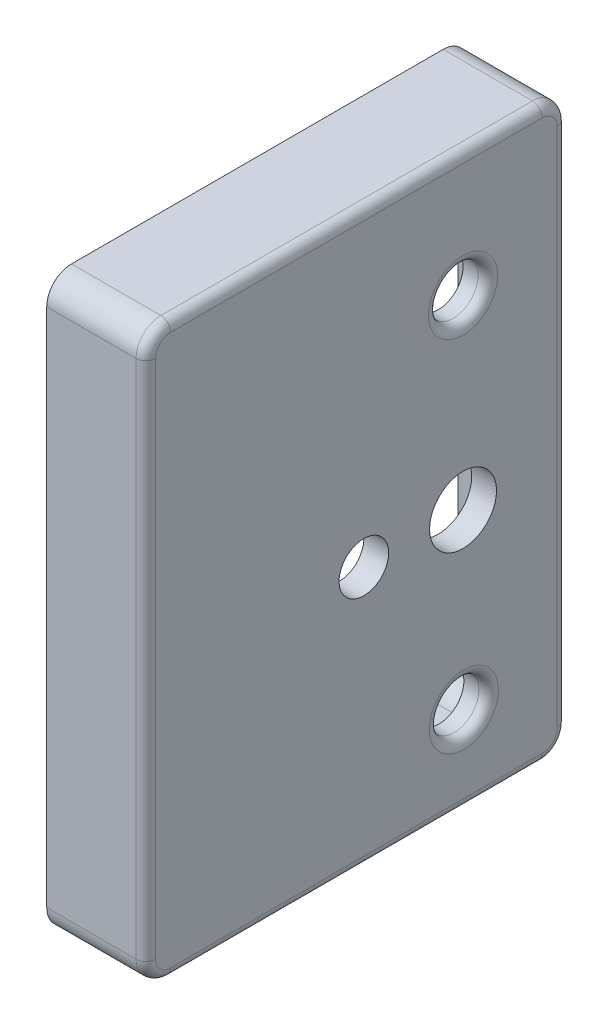
SolidWorks part; units mm, degrees
ref_plane "Front Plane" through (0, 0, 0) normal (0, 0, 1) x (1, 0, 0)
ref_plane "Top Plane" through (0, 0, 0) normal (0, 1, 0) x (1, 0, 0)
ref_plane "Right Plane" through (0, 0, 0) normal (1, 0, 0) x (0, 0, -1)
sketch "Sketch1" plane through (0, 0, 0) normal (1, 0, 0) x (0, 0, -1)
  line L1 (-14.6419, 58.42) -> (28.5381, 58.42)
  line L2 (-14.6419, 58.42) -> (-14.6419, 0)
  line L3 (-14.6419, 0) -> (28.5381, 0)
  line L4 (28.5381, 58.42) -> (28.5381, 0)
  dimension "D1" = 58.42
  dimension "D2" = 43.18
extrude "Boss-Extrude1" add sketch "Sketch1" along normal blind 10.16
sketch "Sketch2" plane through (0, 0, 0) normal (-1, 0, 0) x (0, 0, 1)
  line L0 (14.6419, 0) -> (-28.5381, 0) construction
  line L1 (-25.9981, 3.81) -> (12.1019, 3.81)
  line L2 (-25.9981, 3.81) -> (-25.9981, 49.53)
  line L3 (-25.9981, 49.53) -> (12.1019, 49.53)
  line L4 (12.1019, 3.81) -> (12.1019, 49.53)
  line L5 (-28.5381, 0) -> (-28.5381, 58.42) construction
  line L6 (14.6419, 58.42) -> (14.6419, 0) construction
  circle A0 centre (-17.9669, 8.89) radius 2.54
  circle A1 centre (-17.8811, 45.7198) radius 2.54
  circle A2 centre (-17.8811, 26.6698) radius 3.429
  circle A4 centre (-7.7101, 26.6698) radius 2.54
  dimension "D6" = 5.08
  dimension "D7" = 5.08
  dimension "D8" = 6.858
  dimension "D9" = 19.812
  dimension "D4" = 5.08
  dimension "D2" = 17.78
  dimension "D3" = 19.05
  dimension "D5" = 45.72
  dimension "D10" = 3.81
  dimension "D11" = 2.54
  dimension "D12" = 2.54
  dimension "D14" = 5.08
  dimension "D15" = 17.78
extrude "Cut-Extrude2" cut sketch "Sketch2" against normal through all
sketch "Sketch3" plane through (0, 0, 0) normal (-1, 0, 0) x (0, 0, 1)
  line L0 (-28.5381, 0) -> (-28.5381, 58.42) construction
  line L1 (-26.5061, 2.032) -> (12.6099, 2.032)
  line L2 (-26.5061, 2.032) -> (-26.5061, 56.388)
  line L3 (-26.5061, 56.388) -> (12.6099, 56.388)
  line L4 (12.6099, 2.032) -> (12.6099, 56.388)
  line L5 (14.6419, 58.42) -> (14.6419, 0) construction
  line L6 (-28.5381, 58.42) -> (14.6419, 58.42) construction
  line L7 (14.6419, 0) -> (-28.5381, 0) construction
  dimension "D1" = 2.032
  dimension "D2" = 2.032
  dimension "D3" = 2.032
  dimension "D4" = 2.032
extrude "Cut-Extrude3" cut sketch "Sketch3" against normal blind 7.62
sketch "Sketch4" plane through (0, 0, 0) normal (-1, 0, 0) x (0, 0, 1)
  line L0 (-26.5061, 2.032) -> (12.6099, 2.032) construction
  line L1 (-27.5221, 1.016) -> (13.6259, 1.016)
  line L2 (-27.5221, 1.016) -> (-27.5221, 57.404)
  line L3 (-27.5221, 57.404) -> (13.6259, 57.404)
  line L4 (13.6259, 1.016) -> (13.6259, 57.404)
  line L5 (12.6099, 56.388) -> (-26.5061, 56.388) construction
  line L6 (12.6099, 2.032) -> (12.6099, 56.388) construction
  line L7 (-26.5061, 56.388) -> (-26.5061, 2.032) construction
  dimension "D1" = 1.016
  dimension "D2" = 1.016
  dimension "D3" = 1.016
  dimension "D4" = 1.016
extrude "Cut-Extrude4" cut sketch "Sketch4" against normal blind 3.81
fillet "Fillet1" radius 2.54 2 edges at (1.905, 1.016, -27.5221) (5.715, 2.032, -26.5061)
fillet "Fillet2" radius 2.54 2 edges at (5.715, 2.032, 12.6099) (1.905, 1.016, 13.6259)
fillet "Fillet3" radius 2.54 2 edges at (1.905, 57.404, 13.6259) (5.715, 56.388, 12.6099)
fillet "Fillet4" radius 2.54 2 edges at (1.905, 57.404, -27.5221) (5.715, 56.388, -26.5061)
fillet "Fillet5" radius 2.54 4 edges at (5.08, 0, -28.5381) (5.08, 0, 14.6419) (5.08, 58.42, -28.5381) (5.08, 58.42, 14.6419)
fillet "Fillet6" radius 1 8 edges at (10.16, 0.7439, 13.898) (10.16, 57.6761, 13.898) (10.16, 57.6761, -27.7941) (10.16, 0.7439, -27.7941) (10.16, 29.21, -28.5381) (10.16, 58.42, -6.9481) (10.16, 29.21, 14.6419) (10.16, 0, -6.9481)
fillet "Fillet7" radius 1 1 edges at (10.16, 45.7198, -15.3411)
fillet "Fillet8" radius 1 1 edges at (10.16, 8.89, -15.4269)
